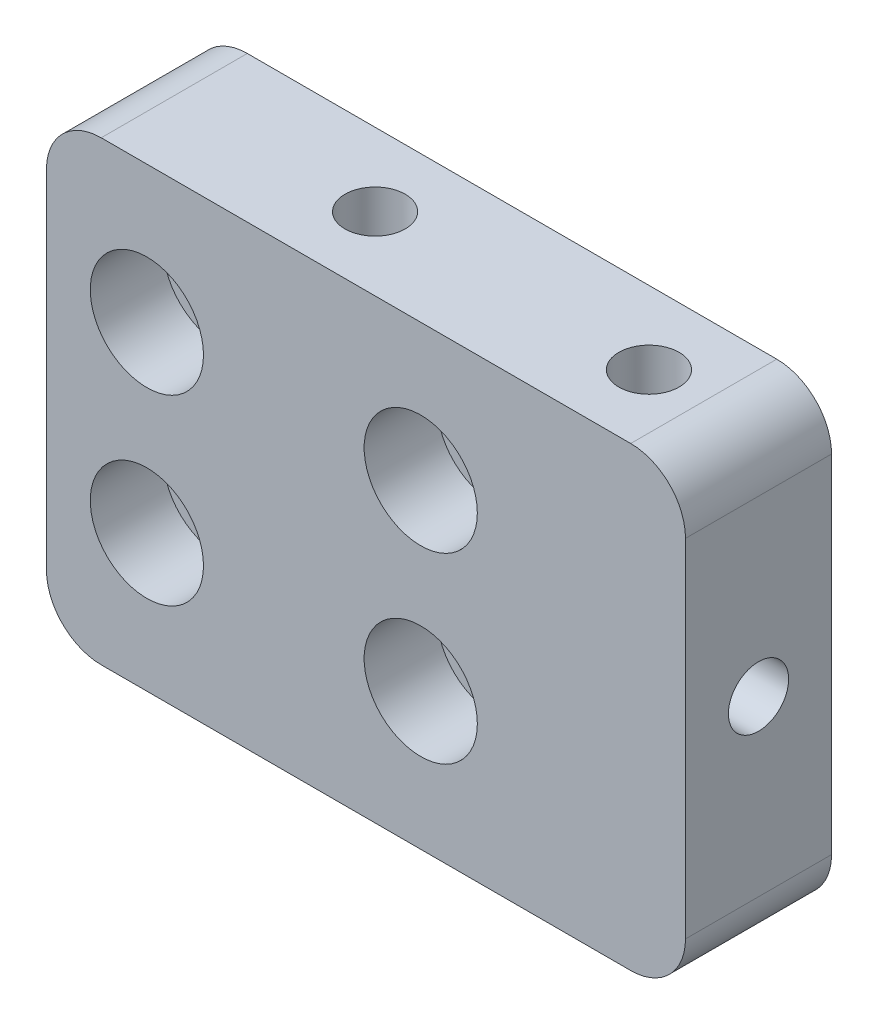
SolidWorks part; units mm, degrees
material "6063-T5"
ref_plane "前视基准面" through (0, 0, 0) normal (0, 0, 1) x (1, 0, 0)
ref_plane "上视基准面" through (0, 0, 0) normal (0, 1, 0) x (1, 0, 0)
ref_plane "右视基准面" through (0, 0, 0) normal (1, 0, 0) x (0, 0, -1)
other "Configuration Table"
sketch "草图1" plane through (0, 0, 0) normal (0, 0, 1) x (1, 0, 0)
  line L1 (-17.5, -12.5) -> (17.5, -12.5)
  line L2 (-17.5, -12.5) -> (-17.5, 12.5)
  line L3 (-17.5, 12.5) -> (17.5, 12.5)
  line L4 (17.5, -12.5) -> (17.5, 12.5)
  line L5 (-17.5, -12.5) -> (17.5, 12.5) construction
  line L6 (-17.5, 12.5) -> (17.5, -12.5) construction
  point P0 (0, 0)
  dimension "D1" = 35
  dimension "D2" = 25
extrude "凸台-拉伸1" add sketch "草图1" along normal blind 8
fillet "圆角1" radius 3 4 edges at (17.5, -12.5, 4) (-17.5, -12.5, 4) (17.5, 12.5, 4) (-17.5, 12.5, 4)
sketch "草图2" plane through (0, 0, 8) normal (0, 0, 1) x (1, 0, 0)
  line L1 (-12, -5) -> (3, -5) construction
  line L2 (-12, -5) -> (-12, 5) construction
  line L3 (-12, 5) -> (3, 5) construction
  line L4 (3, -5) -> (3, 5) construction
  line L5 (-12, -5) -> (3, 5) construction
  line L6 (-12, 5) -> (3, -5) construction
  circle A0 centre (3, 5) radius 1.525
  circle A2 centre (3, -5) radius 1.525
  circle A3 centre (-12, 5) radius 1.525
  circle A4 centre (-12, -5) radius 1.525
  circle A5 centre (-12, 5) radius 1.525 construction
  circle A6 centre (-12, -5) radius 1.525 construction
  circle A7 centre (3, -5) radius 1.2 construction
  point P0 (-4.5, 0)
  dimension "D1" = 3.05
extrude "切除-拉伸1" cut sketch "草图2" against normal through all both and the other way through all
sketch "草图3" plane through (0, 0, 8) normal (0, 0, 1) x (1, 0, 0)
  circle A0 centre (3, 5) radius 3.1
  circle A1 centre (-12, 5) radius 3.1
  circle A2 centre (3, -5) radius 3.1
  circle A3 centre (-12, -5) radius 3.1
  dimension "D1" = 6.2
extrude "切除-拉伸2" cut sketch "草图3" against normal blind 4
sketch "草图4" plane through (0, -12.5, 0) normal (0, -1, 0) x (1, 0, 0)
  point P0 (11.5, 4)
  point P1 (-3.5, 4)
hole_wizard "M4 螺纹孔1" positions "3D草图1" profile "草图5" tap size "M4" standard "GB" end condition through all
sketch3d "3D草图1"
  point P0 (-3.5, -12.5, 4)
  point P3 (11.5, -12.5, 4)
sketch "草图5" plane through (-3.5, -12.5, 4) normal (1, 0, 0) x (0, 0, -1)
  line L0 (0, 0) -> (0, 25)
  line L1 (0, 25) -> (1.65, 25)
  line L2 (1.65, 25) -> (1.65, 0)
  line L5 (1.65, 0) -> (0, 0)
  line L11 (0, -6.35) -> (0, 107.95) construction
  dimension "通孔螺纹孔钻头直径" = 3.3
  dimension "通孔螺纹孔钻头深度" = 25
cosmetic thread "孔螺蚊线1" parameters "D2"=4
cosmetic thread "孔螺蚊线2" parameters "D2"=4
hole_wizard "M4 螺纹孔2" positions "草图7" profile "草图8" tap size "M4" standard "GB" end condition through all
sketch "草图7" plane through (-17.5, 0, 0) normal (-1, 0, 0) x (0, 0, 1)
  point P0 (4, 0)
sketch "草图8" plane through (-17.5, 0, 4) normal (0, 1, 0) x (0, 0, 1)
  line L0 (0, 0) -> (0, 35)
  line L1 (0, 35) -> (1.65, 35)
  line L2 (1.65, 35) -> (1.65, 0)
  line L5 (1.65, 0) -> (0, 0)
  line L11 (0, -6.35) -> (0, 107.95) construction
  dimension "通孔螺纹孔钻头直径" = 3.3
  dimension "通孔螺纹孔钻头深度" = 35
cosmetic thread "孔螺蚊线3" parameters "D2"=4
